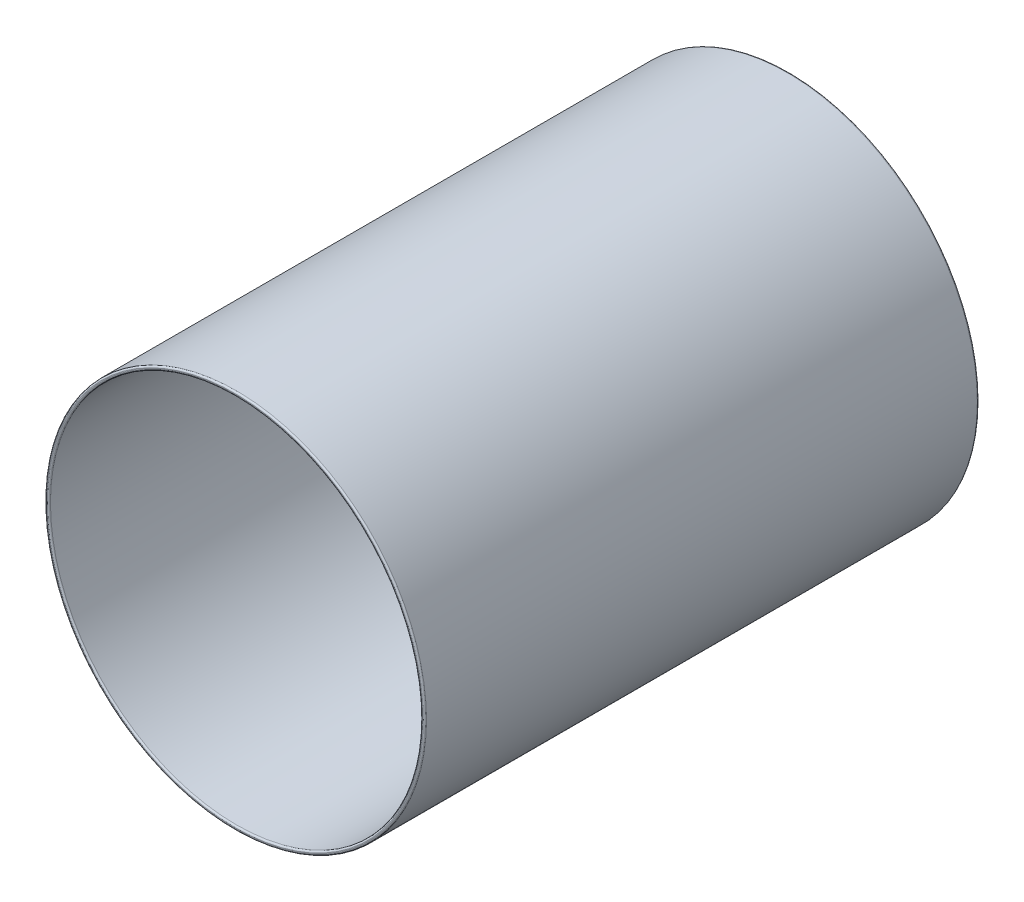
SolidWorks part; units mm, degrees
material "AISI 1035 Steel (SS)"
ref_plane "Front Plane" through (0, 0, 0) normal (0, 0, 1) x (1, 0, 0)
ref_plane "Top Plane" through (0, 0, 0) normal (0, 1, 0) x (1, 0, 0)
ref_plane "Right Plane" through (0, 0, 0) normal (1, 0, 0) x (0, 0, -1)
sketch "Sketch1" plane through (0, 0, 0) normal (0, 0, 1) x (1, 0, 0)
  circle A0 centre (0, 0) radius 240
  circle A1 centre (0, 0) radius 235
  dimension "D1" = 470
  dimension "D2" = 480
extrude "Boss-Extrude1" add sketch "Sketch1" against normal blind 700
fillet "Fillet1" radius 2 4 edges at (235, 0, -700) (240, 0, -700) (235, 0, 0) (240, 0, 0)
